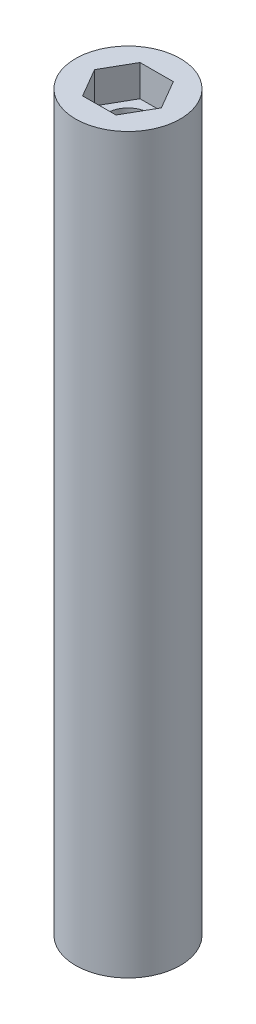
SolidWorks part; units mm, degrees
ref_plane "Front Plane" through (0, 0, 0) normal (0, 0, 1) x (1, 0, 0)
ref_plane "Top Plane" through (0, 0, 0) normal (0, 1, 0) x (1, 0, 0)
ref_plane "Right Plane" through (0, 0, 0) normal (1, 0, 0) x (0, 0, -1)
sketch "Sketch1" plane through (0, 0, 0) normal (0, 1, 0) x (1, 0, 0)
  circle A0 centre (0, 0) radius 5
  dimension "D1" = 10
extrude "Boss-Extrude1" add sketch "Sketch1" along normal blind 70
sketch "Sketch2" plane through (0, 70, 0) normal (0, 1, 0) x (1, 0, 0)
  circle A0 centre (0, 0) radius 2
  dimension "D1" = 4
extrude "Cut-Extrude1" cut sketch "Sketch2" against normal through all
sketch "Sketch3" plane through (0, 70, 0) normal (0, 1, 0) x (1, 0, 0)
  line L1 (1.599, -2.7434) -> (3.1754, 0.0131)
  line L2 (3.1754, 0.0131) -> (1.5764, 2.7565)
  line L3 (1.5764, 2.7565) -> (-1.599, 2.7434)
  line L4 (-1.599, 2.7434) -> (-3.1754, -0.0131)
  line L5 (-3.1754, -0.0131) -> (-1.5764, -2.7565)
  line L6 (-1.5764, -2.7565) -> (1.599, -2.7434)
  circle A0 centre (0, 0) radius 2.75 construction
  dimension "D1" = 5.5
extrude "Cut-Extrude2" cut sketch "Sketch3" against normal blind 3
pattern_linear "LPattern1" count 2 spacing 67 along (0, -1, 0) of "Cut-Extrude2"
